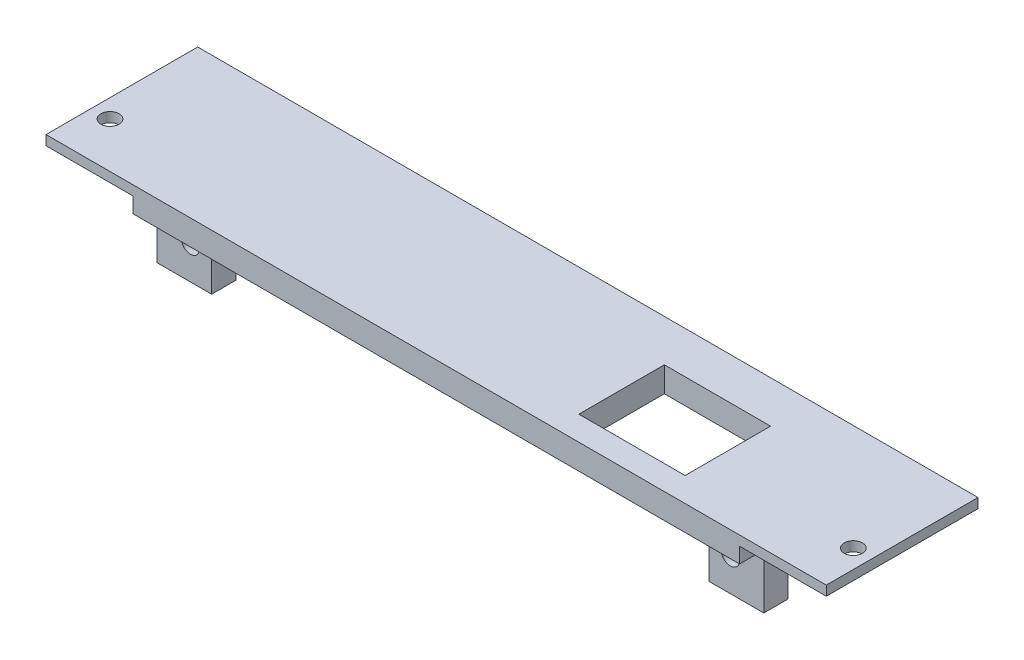
SolidWorks part; units mm, degrees
ref_plane "Front Plane" through (0, 0, 0) normal (0, 0, 1) x (1, 0, 0)
ref_plane "Top Plane" through (0, 0, 0) normal (0, 1, 0) x (1, 0, 0)
ref_plane "Right Plane" through (0, 0, 0) normal (1, 0, 0) x (0, 0, -1)
sketch "Sketch1" plane through (0, 0, 0) normal (0, 1, 0) x (1, 0, 0)
  line L0 (36.5257, -8.0918) -> (36.5257, 4.8343) construction
  line L5 (-64.3, 12.5) -> (64.3, 12.5)
  line L6 (-64.3, 12.5) -> (-64.3, -12.5)
  line L7 (-64.3, -12.5) -> (64.3, -12.5)
  line L8 (64.3, 12.5) -> (64.3, -12.5)
  line L9 (0, -12.5) -> (0, 12.5) construction
  line L10 (-64.3, 0) -> (64.3, 0) construction
  line L11 (20.0177, 4.8343) -> (20.0177, -8.0918) construction
  line L12 (36.5287, 5.0908) -> (20.0187, 5.0908) construction
  line L13 (36.5257, -8.0918) -> (36.5257, 4.8343) construction
  line L14 (20.0177, 4.8343) -> (20.0177, -8.0918) construction
  line L15 (36.5287, 5.0908) -> (20.0187, 5.0908) construction
  line L16 (50, -8.5) -> (-50, -8.5) construction
  line L17 (50, -8.5) -> (-50, -8.5) construction
  line L19 (19.5177, -8.5) -> (37.0257, -8.5)
  line L20 (19.5177, -8.5) -> (19.5177, 5.5908)
  line L21 (19.5177, 5.5908) -> (37.0257, 5.5908)
  line L22 (37.0257, -8.5) -> (37.0257, 5.5908)
  circle A0 centre (-61.25, -5) radius 1.5
  circle A1 centre (61.25, -5) radius 1.5
  point P0 (0, 0)
  dimension "D3" = 61.25
  dimension "D7" = 0.5
  dimension "D1" = 128.6
  dimension "D2" = 25
  dimension "D4" = 61.25
  dimension "D5" = 7.5
  dimension "D6" = 7.5
  dimension "D8" = 0.5
  dimension "D9" = 0.5
extrude "Boss-Extrude1" add sketch "Sketch1" along normal blind 1.6
ref_plane "PCB_back" through (0, -2.54, 0) normal (0, 1, 0) x (1, 0, 0)
ref_plane "PCB_top" through (0, 0, 8.5) normal (0, 0, 1) x (1, 0, 0)
sketch "Sketch3" plane through (0, 0, 0) normal (0, 1, 0) x (1, 0, 0)
  line L0 (64.3, 12.5) -> (-64.3, 12.5) construction
  line L1 (-50, 12.5) -> (50, 12.5)
  line L2 (-50, 12.5) -> (-50, -12.5)
  line L3 (-50, -12.5) -> (50, -12.5)
  line L4 (50, 12.5) -> (50, -12.5)
  line L5 (-64.3, -12.5) -> (64.3, -12.5) construction
  line L6 (-64.3, 12.5) -> (-64.3, -12.5) construction
  line L8 (19.5177, 5.5908) -> (37.0257, 5.5908)
  line L9 (19.5177, 5.5908) -> (19.5177, -8.5)
  line L10 (19.5177, -8.5) -> (37.0257, -8.5)
  line L11 (37.0257, 5.5908) -> (37.0257, -8.5)
  dimension "D1" = 100
  dimension "D2" = 14.3
extrude "Boss-Extrude4" add sketch "Sketch3" against normal blind 2.54
sketch "Sketch4" plane through (0, 0, 8.5) normal (0, 0, 1) x (1, 0, 0)
  line L0 (-50, -2.54) -> (50, -2.54) construction
  line L1 (-50, -2.54) -> (-41, -2.54)
  line L2 (-50, -2.54) -> (-50, -11.54)
  line L3 (-50, -11.54) -> (-41, -11.54)
  line L4 (-41, -2.54) -> (-41, -11.54)
  line L5 (50, -2.54) -> (41, -2.54)
  line L6 (50, -2.54) -> (50, -11.54)
  line L7 (50, -11.54) -> (41, -11.54)
  line L8 (41, -2.54) -> (41, -11.54)
  line L9 (0, -2.277) -> (0, 2.277) construction
  circle A0 centre (44.5, -6.08) radius 1.5
  circle A1 centre (-44.5, -6.08) radius 1.5
  dimension "D1" = 9
  dimension "D2" = 9
  dimension "D3" = 9
  dimension "D4" = 9
  dimension "D5" = 0
  dimension "D6" = 0
  dimension "D7" = 82
  dimension "D8" = 50
  dimension "D9" = 5.5
  dimension "D10" = 3.54
  dimension "D11" = 5.5
  dimension "D12" = 3.54
extrude "Boss-Extrude5" add sketch "Sketch4" against normal blind 4
fillet "Fillet1" radius 2 2 edges at (-45.5, -2.54, 4.5) (45.5, -2.54, 4.5)
equation "\"D10@Sketch4\"=\"D12@Sketch4\""
equation "\"D9@Sketch4\"=\"D11@Sketch4\""
equation "\"D3@Sketch4\"=\"D2@Sketch4\""
